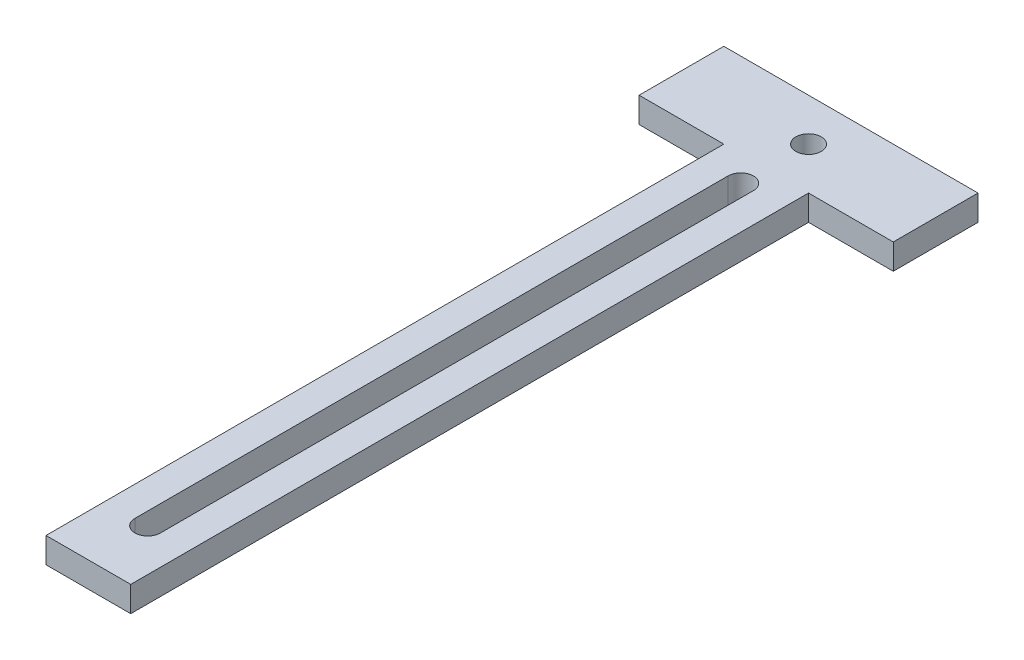
SolidWorks part; units mm, degrees
ref_plane "Front Plane" through (0, 0, 0) normal (0, 0, 1) x (1, 0, 0)
ref_plane "Top Plane" through (0, 0, 0) normal (0, 1, 0) x (1, 0, 0)
ref_plane "Right Plane" through (0, 0, 0) normal (1, 0, 0) x (0, 0, -1)
sketch "Sketch1" plane through (0, 0, 0) normal (0, 1, 0) x (1, 0, 0)
  line L1 (-15, 5) -> (15, 5)
  line L2 (-15, 5) -> (-15, -5)
  line L3 (-15, -5) -> (15, -5)
  line L4 (15, 5) -> (15, -5)
  line L5 (-15, 5) -> (15, -5) construction
  line L6 (-15, -5) -> (15, 5) construction
  circle A0 centre (0, 0) radius 1.5
  point P0 (0, 0)
  dimension "D3" = 3
  dimension "D1" = 10
  dimension "D2" = 30
extrude "Boss-Extrude1" add sketch "Sketch1" along normal blind 3
sketch "Sketch2" plane through (0, 0, 0) normal (0, 1, 0) x (1, 0, 0)
  line L0 (0, -5) -> (5, -5) construction
  line L1 (-15, -5) -> (15, -5) construction
  line L2 (0, -5) -> (0, -8) construction
  line L3 (5, -5) -> (-5, -5)
  line L4 (5, -5) -> (5, -85)
  line L5 (5, -85) -> (-5, -85)
  line L6 (-5, -5) -> (-5, -85)
  line L10 (-1.5, -8) -> (-1.5, -78)
  line L12 (1.5, -8) -> (1.5, -78)
  arc A0 (1.5, -8) -> (-1.5, -8) centre (0, -8) ccw
  arc A1 (-1.5, -78) -> (1.5, -78) centre (0, -78) ccw
  dimension "D8" = 3
  dimension "D5" = 3
  dimension "D1" = 5
  dimension "D2" = 80
  dimension "D3" = 10
  dimension "D4" = 3
  dimension "D6" = 70
  dimension "D7" = 3
extrude "Boss-Extrude2" add sketch "Sketch2" along normal blind 3
